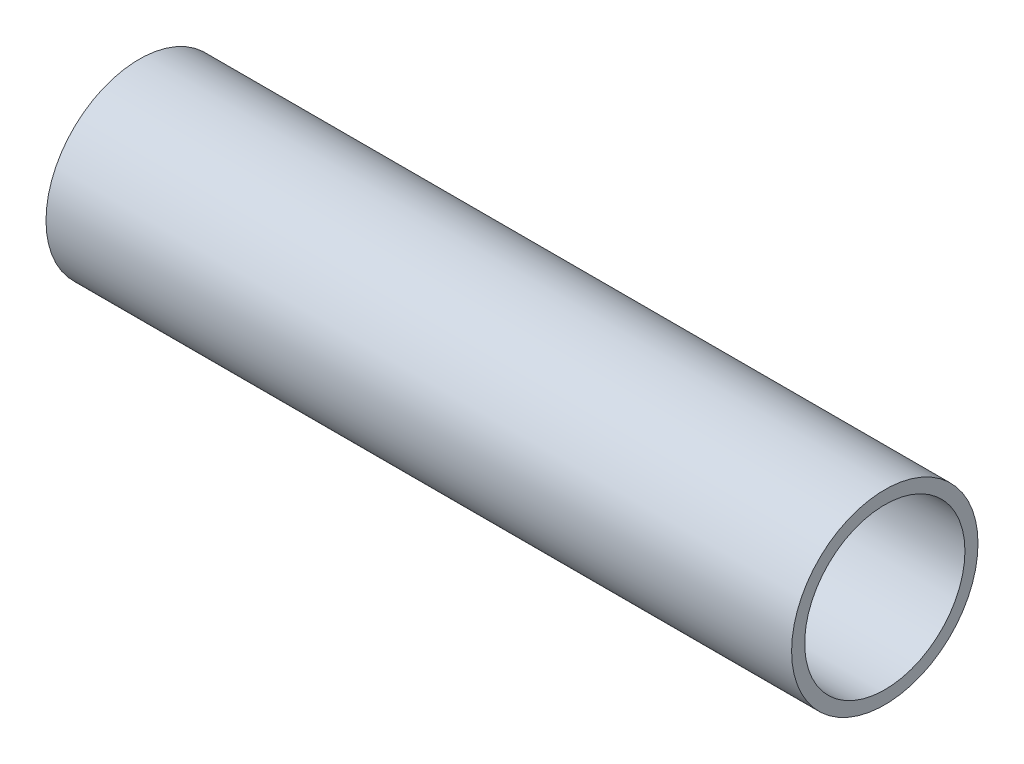
SolidWorks part; units mm, degrees
ref_plane "Front Plane" through (0, 0, 0) normal (0, 0, 1) x (1, 0, 0)
ref_plane "Top Plane" through (0, 0, 0) normal (0, 1, 0) x (1, 0, 0)
ref_plane "Right Plane" through (0, 0, 0) normal (1, 0, 0) x (0, 0, -1)
sketch "Sketch1" plane through (0, 0, 0) normal (1, 0, 0) x (0, 0, -1)
  circle A0 centre (0, 0) radius 6.35
  circle A1 centre (0, 0) radius 5.461
  dimension "D1" = 0.889
  dimension "D2" = 12.7
extrude "Boss-Extrude1" add sketch "Sketch1" along normal blind 50.8
